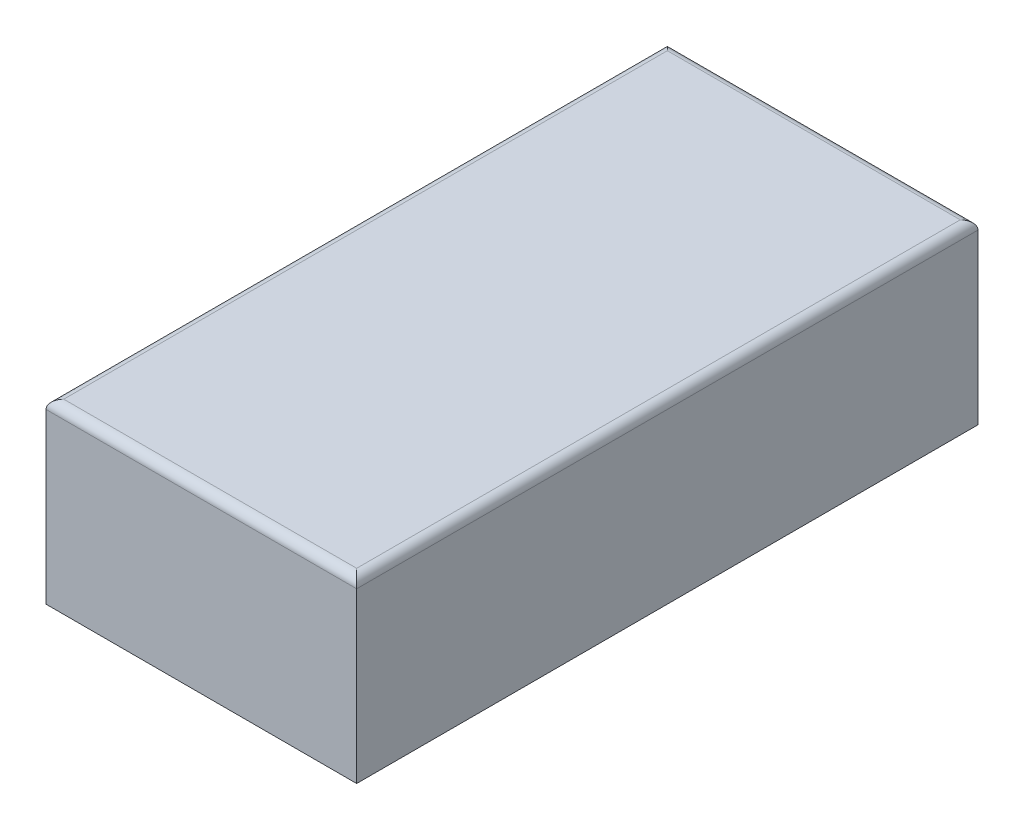
SolidWorks part; units mm, degrees
ref_plane "Front Plane" through (0, 0, 0) normal (0, 0, 1) x (1, 0, 0)
ref_plane "Top Plane" through (0, 0, 0) normal (0, 1, 0) x (1, 0, 0)
ref_plane "Right Plane" through (0, 0, 0) normal (1, 0, 0) x (0, 0, -1)
sketch "Sketch1" plane through (0, 0, 0) normal (0, 1, 0) x (1, 0, 0)
  line L1 (0, 0) -> (3.5, 0)
  line L2 (0, 0) -> (0, 7)
  line L3 (0, 7) -> (3.5, 7)
  line L4 (3.5, 0) -> (3.5, 7)
  dimension "D1" = 7
  dimension "D2" = 3.5
extrude "Boss-Extrude1" add sketch "Sketch1" along normal blind 2
fillet "Fillet1" radius 0.1 4 edges at (1.75, 2, -7) (3.5, 2, -3.5) (1.75, 2, 0) (0, 2, -3.5)
